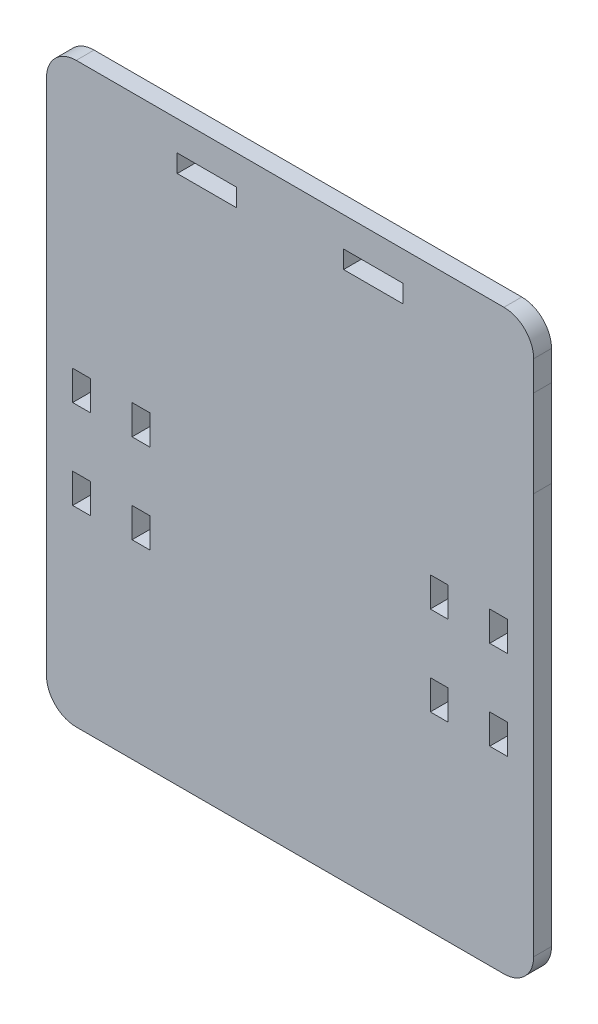
SolidWorks part; units mm, degrees
ref_plane "Alzado" through (0, 0, 0) normal (0, 0, 1) x (1, 0, 0)
ref_plane "Planta" through (0, 0, 0) normal (0, 1, 0) x (1, 0, 0)
ref_plane "Vista lateral" through (0, 0, 0) normal (1, 0, 0) x (0, 0, -1)
sketch "Model" plane through (0, 0, 0) normal (0, 0, 1) x (1, 0, 0)
  line L0 (91.7802, 65.8392) -> (91.7802, 57.38)
  line L1 (9.7833, 46.9338) -> (9.7833, 23.7338)
  line L2 (9.7833, 77.5176) -> (9.7833, 46.9338)
  line L3 (9.7833, 85.5176) -> (9.7833, 77.5176)
  line L4 (86.7802, 90.5176) -> (14.7833, 90.5176)
  line L5 (14.7833, -6.6662) -> (86.7802, -6.6662)
  line L6 (9.7833, 23.7338) -> (9.7833, -1.6662)
  line L7 (91.7802, 57.38) -> (91.7802, 13.1414)
  line L8 (91.7771, 80.5176) -> (91.7802, 85.5176)
  line L9 (91.7802, 65.8392) -> (91.7771, 80.5176)
  line L10 (91.7802, -1.6662) -> (91.7802, 3.6389)
  line L11 (91.7802, 3.6389) -> (91.7802, 13.1414)
  line L12 (59.7802, 85.5176) -> (59.7802, 82.5176)
  line L13 (59.7802, 82.5176) -> (69.7802, 82.5176)
  line L14 (69.7802, 82.5176) -> (69.7802, 85.5176)
  line L15 (69.7802, 85.5176) -> (59.7802, 85.5176)
  line L16 (31.7802, 82.5176) -> (41.7802, 82.5176)
  line L17 (41.7802, 82.5176) -> (41.7802, 85.5176)
  line L18 (41.7802, 85.5176) -> (31.7802, 85.5176)
  line L19 (31.7802, 85.5176) -> (31.7802, 82.5176)
  line L20 (74.3802, 45.3338) -> (77.3802, 45.3338)
  line L21 (74.3802, 40.3338) -> (77.3802, 40.3338)
  line L22 (74.3802, 30.3338) -> (77.3802, 30.3338)
  line L23 (14.1833, 45.3338) -> (17.1833, 45.3338)
  line L24 (14.1833, 40.3338) -> (17.1833, 40.3338)
  line L25 (14.1833, 30.3338) -> (17.1833, 30.3338)
  line L26 (14.1833, 30.3338) -> (17.1833, 30.3338)
  line L27 (84.3802, 40.3338) -> (87.3802, 40.3338)
  line L28 (84.3802, 30.3338) -> (87.3802, 30.3338)
  line L29 (84.3802, 45.3338) -> (87.3802, 45.3338)
  line L30 (24.1833, 40.3338) -> (27.1833, 40.3338)
  line L31 (24.1833, 30.3338) -> (27.1833, 30.3338)
  line L32 (24.1833, 30.3338) -> (27.1833, 30.3338)
  line L33 (24.1833, 45.3338) -> (27.1833, 45.3338)
  line L34 (77.3802, 30.3338) -> (77.3802, 25.3338)
  line L35 (17.1833, 30.3338) -> (17.1833, 25.3338)
  line L36 (87.3802, 30.3338) -> (87.3802, 25.3338)
  line L37 (27.1833, 30.3338) -> (27.1833, 25.3338)
  line L38 (77.3802, 25.3338) -> (74.3802, 25.3338)
  line L39 (17.1833, 30.3338) -> (14.1833, 30.3338)
  line L40 (17.1833, 25.3338) -> (14.1833, 25.3338)
  line L41 (87.3802, 25.3338) -> (84.3802, 25.3338)
  line L42 (87.3802, 30.3338) -> (84.3802, 30.3338)
  line L43 (27.1833, 25.3338) -> (24.1833, 25.3338)
  line L44 (27.1833, 30.3338) -> (24.1833, 30.3338)
  line L45 (77.3802, 30.3338) -> (74.3802, 30.3338)
  line L46 (14.1833, 25.3338) -> (14.1833, 30.3338)
  line L47 (84.3802, 25.3338) -> (84.3802, 30.3338)
  line L48 (24.1833, 25.3338) -> (24.1833, 30.3338)
  line L49 (74.3802, 25.3338) -> (74.3802, 30.3338)
  line L50 (14.1833, 40.3338) -> (14.1833, 45.3338)
  line L51 (84.3802, 40.3338) -> (84.3802, 45.3338)
  line L52 (24.1833, 40.3338) -> (24.1833, 45.3338)
  line L53 (74.3802, 40.3338) -> (74.3802, 45.3338)
  line L54 (17.1833, 45.3338) -> (17.1833, 40.3338)
  line L55 (87.3802, 45.3338) -> (87.3802, 40.3338)
  line L56 (27.1833, 45.3338) -> (27.1833, 40.3338)
  line L57 (77.3802, 45.3338) -> (77.3802, 40.3338)
  arc A0 (14.7833, 90.5176) -> (9.7833, 85.5176) centre (14.7833, 85.5176) ccw
  arc A1 (9.7833, -1.6662) -> (14.7833, -6.6662) centre (14.7833, -1.6662) ccw
  arc A2 (91.7802, 85.5176) -> (86.7802, 90.5176) centre (86.7802, 85.5176) ccw
  arc A3 (86.7802, -6.6662) -> (91.7802, -1.6662) centre (86.7802, -1.6662) ccw
extrude "Saliente-Extruir1" add sketch "Model" along normal blind 3 contours L5 A3 L10 L11 L7 L0 L9 L8 A2 L4 A0 L3 L2 L1 L6 A1 L20 L57 L21 L53 L33 L56 L30 L52 L29 L55 L27 L51 L23 L54 L24 L50 L38 L49 L22 L34 L43 L48 L31 L37 L41 L47 L28 L36
